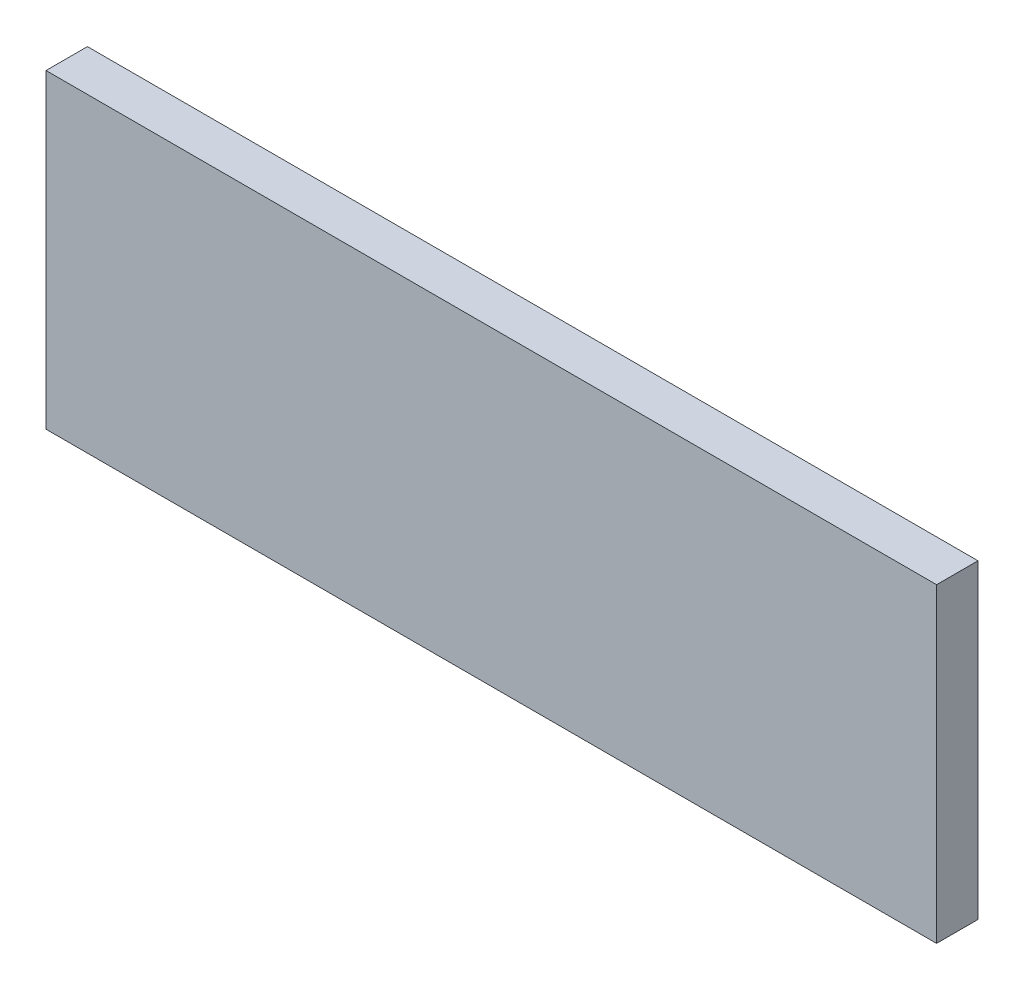
SolidWorks part; units mm, degrees
ref_plane "Front Plane" through (0, 0, 0) normal (0, 0, 1) x (1, 0, 0)
ref_plane "Top Plane" through (0, 0, 0) normal (0, 1, 0) x (1, 0, 0)
ref_plane "Right Plane" through (0, 0, 0) normal (1, 0, 0) x (0, 0, -1)
sketch "Sketch1" plane through (0, 0, 0) normal (0, 0, 1) x (1, 0, 0)
  line L1 (0, 0) -> (109.22, 0)
  line L2 (0, 0) -> (0, 38.1)
  line L3 (0, 38.1) -> (109.22, 38.1)
  line L4 (109.22, 0) -> (109.22, 38.1)
  dimension "D1" = 38.1
  dimension "D2" = 109.22
extrude "Boss-Extrude1" add sketch "Sketch1" along normal blind 5.08
